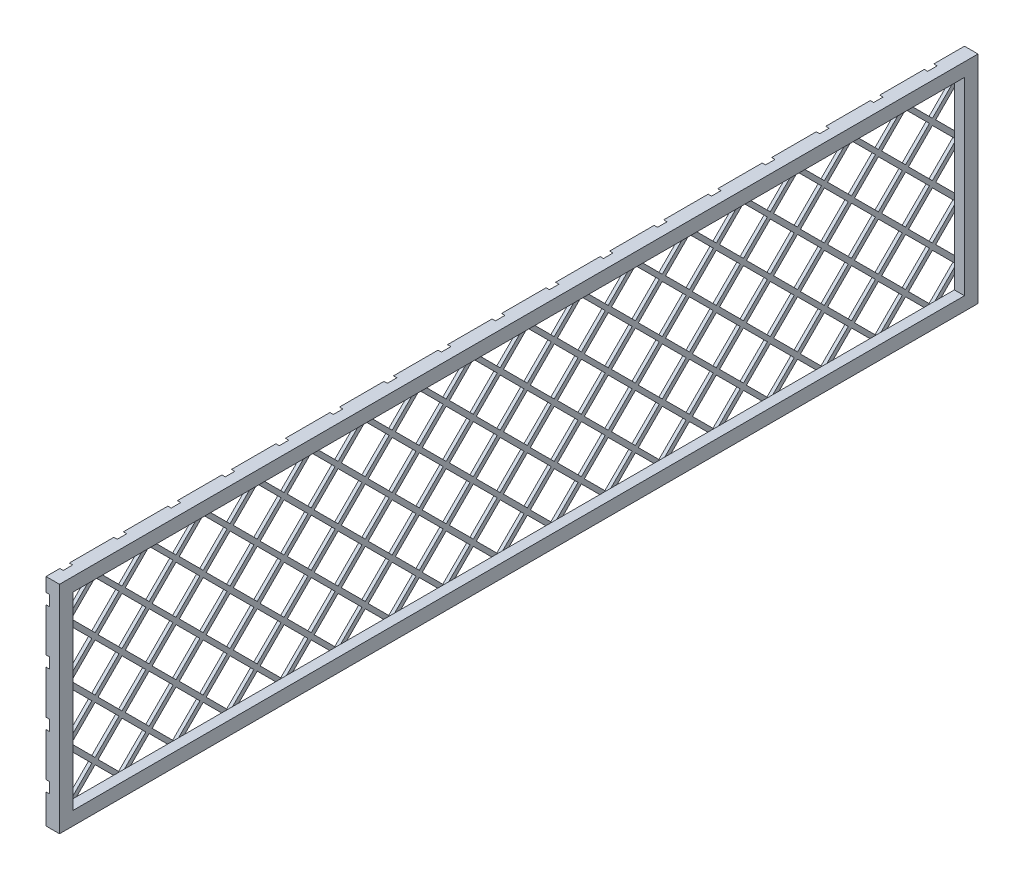
SolidWorks part; units mm, degrees
ref_plane "Front" through (0, 0, 0) normal (0, 0, 1) x (1, 0, 0)
ref_plane "Top" through (0, 0, 0) normal (0, 1, 0) x (1, 0, 0)
ref_plane "Right" through (0, 0, 0) normal (1, 0, 0) x (0, 0, -1)
sketch "Sketch1" plane through (0, 0, 0) normal (1, 0, 0) x (0, 0, -1)
  line L1 (-344.8454, 224.4468) -> (518.7546, 224.4468)
  line L2 (-344.8454, 224.4468) -> (-344.8454, 21.2468)
  line L3 (-344.8454, 21.2468) -> (518.7546, 21.2468)
  line L4 (518.7546, 224.4468) -> (518.7546, 21.2468)
  line L5 (-332.1454, 211.7468) -> (506.0546, 211.7468)
  line L6 (-332.1454, 211.7468) -> (-332.1454, 33.9468)
  line L7 (-332.1454, 33.9468) -> (506.0546, 33.9468)
  line L8 (506.0546, 211.7468) -> (506.0546, 33.9468)
  dimension "D1" = 863.6
  dimension "D2" = 203.2
  dimension "D3" = 12.7
  dimension "D4" = 12.7
  dimension "D5" = 12.7
  dimension "D6" = 12.7
extrude "Boss-Extrude1" add sketch "Sketch1" along normal blind 12.7
sketch "Sketch2" plane through (0, 0, 0) normal (-1, 0, 0) x (0, 0, 1)
  line L1 (-506.0546, 211.7468) -> (332.1454, 211.7468)
  line L2 (-506.0546, 211.7468) -> (-506.0546, 33.9468)
  line L3 (-506.0546, 33.9468) -> (332.1454, 33.9468)
  line L4 (332.1454, 211.7468) -> (332.1454, 33.9468)
extrude "Boss-Extrude2" add sketch "Sketch2" against normal blind 3.175
sketch "Sketch3" plane through (3.175, 0, 0) normal (1, 0, 0) x (0, 0, -1)
  line L0 (-324.2862, 181.2013) -> (-301.8355, 203.6519)
  line L1 (-301.8355, 203.6519) -> (-279.3849, 181.2013)
  line L2 (-324.2862, 181.2013) -> (-301.8355, 158.7506)
  line L3 (-301.8355, 158.7506) -> (-279.3849, 181.2013)
  line L4 (-276.5793, 178.1081) -> (-254.1286, 155.6575)
  line L5 (-254.1286, 155.6575) -> (-276.5793, 133.2069)
  line L6 (-276.5793, 133.2069) -> (-299.0299, 155.6575)
  line L7 (-299.0299, 155.6575) -> (-276.5793, 178.1081)
  line L8 (-327.3793, 228.9081) -> (-304.9286, 206.4575)
  line L9 (-304.9286, 206.4575) -> (-327.3793, 184.0069)
  line L10 (-327.3793, 184.0069) -> (-349.8299, 206.4575)
  line L11 (-349.8299, 206.4575) -> (-327.3793, 228.9081)
  line L12 (-276.5793, 228.9081) -> (-254.1286, 206.4575)
  line L13 (-254.1286, 206.4575) -> (-276.5793, 184.0069)
  line L14 (-276.5793, 184.0069) -> (-299.0299, 206.4575)
  line L15 (-299.0299, 206.4575) -> (-276.5793, 228.9081)
  line L16 (-254.1286, 206.4575) -> (-276.5793, 184.0069)
  line L17 (-276.5793, 184.0069) -> (-299.0299, 206.4575)
  line L18 (-299.0299, 206.4575) -> (-276.5793, 228.9081)
  line L19 (-276.5793, 228.9081) -> (-254.1286, 206.4575)
  line L20 (-251.0355, 203.6519) -> (-228.5849, 181.2013)
  line L21 (-273.4862, 181.2013) -> (-251.0355, 203.6519)
  line L22 (-273.4862, 181.2013) -> (-251.0355, 158.7506)
  line L23 (-251.0355, 158.7506) -> (-228.5849, 181.2013)
  line L24 (-203.3286, 206.4575) -> (-225.7793, 184.0069)
  line L25 (-225.7793, 184.0069) -> (-248.2299, 206.4575)
  line L26 (-248.2299, 206.4575) -> (-225.7793, 228.9081)
  line L27 (-225.7793, 228.9081) -> (-203.3286, 206.4575)
  line L28 (-200.2355, 203.6519) -> (-177.7849, 181.2013)
  line L29 (-222.6862, 181.2013) -> (-200.2355, 203.6519)
  line L30 (-222.6862, 181.2013) -> (-200.2355, 158.7506)
  line L31 (-200.2355, 158.7506) -> (-177.7849, 181.2013)
  line L32 (-152.5286, 206.4575) -> (-174.9793, 184.0069)
  line L33 (-174.9793, 184.0069) -> (-197.4299, 206.4575)
  line L34 (-197.4299, 206.4575) -> (-174.9793, 228.9081)
  line L35 (-174.9793, 228.9081) -> (-152.5286, 206.4575)
  line L36 (-149.4355, 203.6519) -> (-126.9849, 181.2013)
  line L37 (-171.8862, 181.2013) -> (-149.4355, 203.6519)
  line L38 (-171.8862, 181.2013) -> (-149.4355, 158.7506)
  line L39 (-149.4355, 158.7506) -> (-126.9849, 181.2013)
  line L40 (-101.7286, 206.4575) -> (-124.1793, 184.0069)
  line L41 (-124.1793, 184.0069) -> (-146.6299, 206.4575)
  line L42 (-146.6299, 206.4575) -> (-124.1793, 228.9081)
  line L43 (-124.1793, 228.9081) -> (-101.7286, 206.4575)
  line L44 (-98.6355, 203.6519) -> (-76.1849, 181.2013)
  line L45 (-121.0862, 181.2013) -> (-98.6355, 203.6519)
  line L46 (-121.0862, 181.2013) -> (-98.6355, 158.7506)
  line L47 (-98.6355, 158.7506) -> (-76.1849, 181.2013)
  line L48 (-50.9286, 206.4575) -> (-73.3793, 184.0069)
  line L49 (-73.3793, 184.0069) -> (-95.8299, 206.4575)
  line L50 (-95.8299, 206.4575) -> (-73.3793, 228.9081)
  line L51 (-73.3793, 228.9081) -> (-50.9286, 206.4575)
  line L52 (-47.8355, 203.6519) -> (-25.3849, 181.2013)
  line L53 (-70.2862, 181.2013) -> (-47.8355, 203.6519)
  line L54 (-70.2862, 181.2013) -> (-47.8355, 158.7506)
  line L55 (-47.8355, 158.7506) -> (-25.3849, 181.2013)
  line L56 (-0.1286, 206.4575) -> (-22.5793, 184.0069)
  line L57 (-22.5793, 184.0069) -> (-45.0299, 206.4575)
  line L58 (-45.0299, 206.4575) -> (-22.5793, 228.9081)
  line L59 (-22.5793, 228.9081) -> (-0.1286, 206.4575)
  line L60 (2.9645, 203.6519) -> (25.4151, 181.2013)
  line L61 (-19.4862, 181.2013) -> (2.9645, 203.6519)
  line L62 (-19.4862, 181.2013) -> (2.9645, 158.7506)
  line L63 (2.9645, 158.7506) -> (25.4151, 181.2013)
  line L64 (50.6714, 206.4575) -> (28.2207, 184.0069)
  line L65 (28.2207, 184.0069) -> (5.7701, 206.4575)
  line L66 (5.7701, 206.4575) -> (28.2207, 228.9081)
  line L67 (28.2207, 228.9081) -> (50.6714, 206.4575)
  line L68 (53.7645, 203.6519) -> (76.2151, 181.2013)
  line L69 (31.3138, 181.2013) -> (53.7645, 203.6519)
  line L70 (31.3138, 181.2013) -> (53.7645, 158.7506)
  line L71 (53.7645, 158.7506) -> (76.2151, 181.2013)
  line L72 (101.4714, 206.4575) -> (79.0207, 184.0069)
  line L73 (79.0207, 184.0069) -> (56.5701, 206.4575)
  line L74 (56.5701, 206.4575) -> (79.0207, 228.9081)
  line L75 (79.0207, 228.9081) -> (101.4714, 206.4575)
  line L76 (104.5645, 203.6519) -> (127.0151, 181.2013)
  line L77 (82.1138, 181.2013) -> (104.5645, 203.6519)
  line L78 (82.1138, 181.2013) -> (104.5645, 158.7506)
  line L79 (104.5645, 158.7506) -> (127.0151, 181.2013)
  line L80 (152.2714, 206.4575) -> (129.8207, 184.0069)
  line L81 (129.8207, 184.0069) -> (107.3701, 206.4575)
  line L82 (107.3701, 206.4575) -> (129.8207, 228.9081)
  line L83 (129.8207, 228.9081) -> (152.2714, 206.4575)
  line L84 (155.3645, 203.6519) -> (177.8151, 181.2013)
  line L85 (132.9138, 181.2013) -> (155.3645, 203.6519)
  line L86 (132.9138, 181.2013) -> (155.3645, 158.7506)
  line L87 (155.3645, 158.7506) -> (177.8151, 181.2013)
  line L88 (203.0714, 206.4575) -> (180.6207, 184.0069)
  line L89 (180.6207, 184.0069) -> (158.1701, 206.4575)
  line L90 (158.1701, 206.4575) -> (180.6207, 228.9081)
  line L91 (180.6207, 228.9081) -> (203.0714, 206.4575)
  line L92 (206.1645, 203.6519) -> (228.6151, 181.2013)
  line L93 (183.7138, 181.2013) -> (206.1645, 203.6519)
  line L94 (183.7138, 181.2013) -> (206.1645, 158.7506)
  line L95 (206.1645, 158.7506) -> (228.6151, 181.2013)
  line L96 (253.8714, 206.4575) -> (231.4207, 184.0069)
  line L97 (231.4207, 184.0069) -> (208.9701, 206.4575)
  line L98 (208.9701, 206.4575) -> (231.4207, 228.9081)
  line L99 (231.4207, 228.9081) -> (253.8714, 206.4575)
  line L100 (256.9645, 203.6519) -> (279.4151, 181.2013)
  line L101 (234.5138, 181.2013) -> (256.9645, 203.6519)
  line L102 (234.5138, 181.2013) -> (256.9645, 158.7506)
  line L103 (256.9645, 158.7506) -> (279.4151, 181.2013)
  line L104 (304.6714, 206.4575) -> (282.2207, 184.0069)
  line L105 (282.2207, 184.0069) -> (259.7701, 206.4575)
  line L106 (259.7701, 206.4575) -> (282.2207, 228.9081)
  line L107 (282.2207, 228.9081) -> (304.6714, 206.4575)
  line L108 (307.7645, 203.6519) -> (330.2151, 181.2013)
  line L109 (285.3138, 181.2013) -> (307.7645, 203.6519)
  line L110 (285.3138, 181.2013) -> (307.7645, 158.7506)
  line L111 (307.7645, 158.7506) -> (330.2151, 181.2013)
  line L112 (355.4714, 206.4575) -> (333.0207, 184.0069)
  line L113 (333.0207, 184.0069) -> (310.5701, 206.4575)
  line L114 (310.5701, 206.4575) -> (333.0207, 228.9081)
  line L115 (333.0207, 228.9081) -> (355.4714, 206.4575)
  line L116 (358.5645, 203.6519) -> (381.0151, 181.2013)
  line L117 (336.1138, 181.2013) -> (358.5645, 203.6519)
  line L118 (336.1138, 181.2013) -> (358.5645, 158.7506)
  line L119 (358.5645, 158.7506) -> (381.0151, 181.2013)
  line L120 (406.2714, 206.4575) -> (383.8207, 184.0069)
  line L121 (383.8207, 184.0069) -> (361.3701, 206.4575)
  line L122 (361.3701, 206.4575) -> (383.8207, 228.9081)
  line L123 (383.8207, 228.9081) -> (406.2714, 206.4575)
  line L124 (409.3645, 203.6519) -> (431.8151, 181.2013)
  line L125 (386.9138, 181.2013) -> (409.3645, 203.6519)
  line L126 (386.9138, 181.2013) -> (409.3645, 158.7506)
  line L127 (409.3645, 158.7506) -> (431.8151, 181.2013)
  line L128 (457.0714, 206.4575) -> (434.6207, 184.0069)
  line L129 (434.6207, 184.0069) -> (412.1701, 206.4575)
  line L130 (412.1701, 206.4575) -> (434.6207, 228.9081)
  line L131 (434.6207, 228.9081) -> (457.0714, 206.4575)
  line L132 (460.1645, 203.6519) -> (482.6151, 181.2013)
  line L133 (437.7138, 181.2013) -> (460.1645, 203.6519)
  line L134 (437.7138, 181.2013) -> (460.1645, 158.7506)
  line L135 (460.1645, 158.7506) -> (482.6151, 181.2013)
  line L136 (507.8714, 206.4575) -> (485.4207, 184.0069)
  line L137 (485.4207, 184.0069) -> (462.9701, 206.4575)
  line L138 (462.9701, 206.4575) -> (485.4207, 228.9081)
  line L139 (485.4207, 228.9081) -> (507.8714, 206.4575)
  line L140 (510.9645, 203.6519) -> (533.4151, 181.2013)
  line L141 (488.5138, 181.2013) -> (510.9645, 203.6519)
  line L142 (488.5138, 181.2013) -> (510.9645, 158.7506)
  line L143 (510.9645, 158.7506) -> (533.4151, 181.2013)
  line L144 (-254.1286, 155.6575) -> (-276.5793, 133.2069)
  line L145 (-276.5793, 133.2069) -> (-299.0299, 155.6575)
  line L146 (-299.0299, 155.6575) -> (-276.5793, 178.1081)
  line L147 (-276.5793, 178.1081) -> (-254.1286, 155.6575)
  line L148 (-251.0355, 152.8519) -> (-228.5849, 130.4013)
  line L149 (-273.4862, 130.4013) -> (-251.0355, 152.8519)
  line L150 (-273.4862, 130.4013) -> (-251.0355, 107.9506)
  line L151 (-251.0355, 107.9506) -> (-228.5849, 130.4013)
  line L152 (-203.3286, 155.6575) -> (-225.7793, 133.2069)
  line L153 (-225.7793, 133.2069) -> (-248.2299, 155.6575)
  line L154 (-248.2299, 155.6575) -> (-225.7793, 178.1081)
  line L155 (-225.7793, 178.1081) -> (-203.3286, 155.6575)
  line L156 (-200.2355, 152.8519) -> (-177.7849, 130.4013)
  line L157 (-222.6862, 130.4013) -> (-200.2355, 152.8519)
  line L158 (-222.6862, 130.4013) -> (-200.2355, 107.9506)
  line L159 (-200.2355, 107.9506) -> (-177.7849, 130.4013)
  line L160 (-152.5286, 155.6575) -> (-174.9793, 133.2069)
  line L161 (-174.9793, 133.2069) -> (-197.4299, 155.6575)
  line L162 (-197.4299, 155.6575) -> (-174.9793, 178.1081)
  line L163 (-174.9793, 178.1081) -> (-152.5286, 155.6575)
  line L164 (-149.4355, 152.8519) -> (-126.9849, 130.4013)
  line L165 (-171.8862, 130.4013) -> (-149.4355, 152.8519)
  line L166 (-171.8862, 130.4013) -> (-149.4355, 107.9506)
  line L167 (-149.4355, 107.9506) -> (-126.9849, 130.4013)
  line L168 (-101.7286, 155.6575) -> (-124.1793, 133.2069)
  line L169 (-124.1793, 133.2069) -> (-146.6299, 155.6575)
  line L170 (-146.6299, 155.6575) -> (-124.1793, 178.1081)
  line L171 (-124.1793, 178.1081) -> (-101.7286, 155.6575)
  line L172 (-98.6355, 152.8519) -> (-76.1849, 130.4013)
  line L173 (-121.0862, 130.4013) -> (-98.6355, 152.8519)
  line L174 (-121.0862, 130.4013) -> (-98.6355, 107.9506)
  line L175 (-98.6355, 107.9506) -> (-76.1849, 130.4013)
  line L176 (-50.9286, 155.6575) -> (-73.3793, 133.2069)
  line L177 (-73.3793, 133.2069) -> (-95.8299, 155.6575)
  line L178 (-95.8299, 155.6575) -> (-73.3793, 178.1081)
  line L179 (-73.3793, 178.1081) -> (-50.9286, 155.6575)
  line L180 (-47.8355, 152.8519) -> (-25.3849, 130.4013)
  line L181 (-70.2862, 130.4013) -> (-47.8355, 152.8519)
  line L182 (-70.2862, 130.4013) -> (-47.8355, 107.9506)
  line L183 (-47.8355, 107.9506) -> (-25.3849, 130.4013)
  line L184 (-0.1286, 155.6575) -> (-22.5793, 133.2069)
  line L185 (-22.5793, 133.2069) -> (-45.0299, 155.6575)
  line L186 (-45.0299, 155.6575) -> (-22.5793, 178.1081)
  line L187 (-22.5793, 178.1081) -> (-0.1286, 155.6575)
  line L188 (2.9645, 152.8519) -> (25.4151, 130.4013)
  line L189 (-19.4862, 130.4013) -> (2.9645, 152.8519)
  line L190 (-19.4862, 130.4013) -> (2.9645, 107.9506)
  line L191 (2.9645, 107.9506) -> (25.4151, 130.4013)
  line L192 (50.6714, 155.6575) -> (28.2207, 133.2069)
  line L193 (28.2207, 133.2069) -> (5.7701, 155.6575)
  line L194 (5.7701, 155.6575) -> (28.2207, 178.1081)
  line L195 (28.2207, 178.1081) -> (50.6714, 155.6575)
  line L196 (53.7645, 152.8519) -> (76.2151, 130.4013)
  line L197 (31.3138, 130.4013) -> (53.7645, 152.8519)
  line L198 (31.3138, 130.4013) -> (53.7645, 107.9506)
  line L199 (53.7645, 107.9506) -> (76.2151, 130.4013)
  line L200 (101.4714, 155.6575) -> (79.0207, 133.2069)
  line L201 (79.0207, 133.2069) -> (56.5701, 155.6575)
  line L202 (56.5701, 155.6575) -> (79.0207, 178.1081)
  line L203 (79.0207, 178.1081) -> (101.4714, 155.6575)
  line L204 (104.5645, 152.8519) -> (127.0151, 130.4013)
  line L205 (82.1138, 130.4013) -> (104.5645, 152.8519)
  line L206 (82.1138, 130.4013) -> (104.5645, 107.9506)
  line L207 (104.5645, 107.9506) -> (127.0151, 130.4013)
  line L208 (152.2714, 155.6575) -> (129.8207, 133.2069)
  line L209 (129.8207, 133.2069) -> (107.3701, 155.6575)
  line L210 (107.3701, 155.6575) -> (129.8207, 178.1081)
  line L211 (129.8207, 178.1081) -> (152.2714, 155.6575)
  line L212 (155.3645, 152.8519) -> (177.8151, 130.4013)
  line L213 (132.9138, 130.4013) -> (155.3645, 152.8519)
  line L214 (132.9138, 130.4013) -> (155.3645, 107.9506)
  line L215 (155.3645, 107.9506) -> (177.8151, 130.4013)
  line L216 (203.0714, 155.6575) -> (180.6207, 133.2069)
  line L217 (180.6207, 133.2069) -> (158.1701, 155.6575)
  line L218 (158.1701, 155.6575) -> (180.6207, 178.1081)
  line L219 (180.6207, 178.1081) -> (203.0714, 155.6575)
  line L220 (206.1645, 152.8519) -> (228.6151, 130.4013)
  line L221 (183.7138, 130.4013) -> (206.1645, 152.8519)
  line L222 (183.7138, 130.4013) -> (206.1645, 107.9506)
  line L223 (206.1645, 107.9506) -> (228.6151, 130.4013)
  line L224 (253.8714, 155.6575) -> (231.4207, 133.2069)
  line L225 (231.4207, 133.2069) -> (208.9701, 155.6575)
  line L226 (208.9701, 155.6575) -> (231.4207, 178.1081)
  line L227 (231.4207, 178.1081) -> (253.8714, 155.6575)
  line L228 (256.9645, 152.8519) -> (279.4151, 130.4013)
  line L229 (234.5138, 130.4013) -> (256.9645, 152.8519)
  line L230 (234.5138, 130.4013) -> (256.9645, 107.9506)
  line L231 (256.9645, 107.9506) -> (279.4151, 130.4013)
  line L232 (304.6714, 155.6575) -> (282.2207, 133.2069)
  line L233 (282.2207, 133.2069) -> (259.7701, 155.6575)
  line L234 (259.7701, 155.6575) -> (282.2207, 178.1081)
  line L235 (282.2207, 178.1081) -> (304.6714, 155.6575)
  line L236 (307.7645, 152.8519) -> (330.2151, 130.4013)
  line L237 (285.3138, 130.4013) -> (307.7645, 152.8519)
  line L238 (285.3138, 130.4013) -> (307.7645, 107.9506)
  line L239 (307.7645, 107.9506) -> (330.2151, 130.4013)
  line L240 (355.4714, 155.6575) -> (333.0207, 133.2069)
  line L241 (333.0207, 133.2069) -> (310.5701, 155.6575)
  line L242 (310.5701, 155.6575) -> (333.0207, 178.1081)
  line L243 (333.0207, 178.1081) -> (355.4714, 155.6575)
  line L244 (358.5645, 152.8519) -> (381.0151, 130.4013)
  line L245 (336.1138, 130.4013) -> (358.5645, 152.8519)
  line L246 (336.1138, 130.4013) -> (358.5645, 107.9506)
  line L247 (358.5645, 107.9506) -> (381.0151, 130.4013)
  line L248 (406.2714, 155.6575) -> (383.8207, 133.2069)
  line L249 (383.8207, 133.2069) -> (361.3701, 155.6575)
  line L250 (361.3701, 155.6575) -> (383.8207, 178.1081)
  line L251 (383.8207, 178.1081) -> (406.2714, 155.6575)
  line L252 (409.3645, 152.8519) -> (431.8151, 130.4013)
  line L253 (386.9138, 130.4013) -> (409.3645, 152.8519)
  line L254 (386.9138, 130.4013) -> (409.3645, 107.9506)
  line L255 (409.3645, 107.9506) -> (431.8151, 130.4013)
  line L256 (457.0714, 155.6575) -> (434.6207, 133.2069)
  line L257 (434.6207, 133.2069) -> (412.1701, 155.6575)
  line L258 (412.1701, 155.6575) -> (434.6207, 178.1081)
  line L259 (434.6207, 178.1081) -> (457.0714, 155.6575)
  line L260 (460.1645, 152.8519) -> (482.6151, 130.4013)
  line L261 (437.7138, 130.4013) -> (460.1645, 152.8519)
  line L262 (437.7138, 130.4013) -> (460.1645, 107.9506)
  line L263 (460.1645, 107.9506) -> (482.6151, 130.4013)
  line L264 (507.8714, 155.6575) -> (485.4207, 133.2069)
  line L265 (485.4207, 133.2069) -> (462.9701, 155.6575)
  line L266 (462.9701, 155.6575) -> (485.4207, 178.1081)
  line L267 (485.4207, 178.1081) -> (507.8714, 155.6575)
  line L268 (510.9645, 152.8519) -> (533.4151, 130.4013)
  line L269 (488.5138, 130.4013) -> (510.9645, 152.8519)
  line L270 (488.5138, 130.4013) -> (510.9645, 107.9506)
  line L271 (510.9645, 107.9506) -> (533.4151, 130.4013)
  line L272 (-254.1286, 104.8575) -> (-276.5793, 82.4069)
  line L273 (-276.5793, 82.4069) -> (-299.0299, 104.8575)
  line L274 (-299.0299, 104.8575) -> (-276.5793, 127.3081)
  line L275 (-276.5793, 127.3081) -> (-254.1286, 104.8575)
  line L276 (-251.0355, 102.0519) -> (-228.5849, 79.6013)
  line L277 (-273.4862, 79.6013) -> (-251.0355, 102.0519)
  line L278 (-273.4862, 79.6013) -> (-251.0355, 57.1506)
  line L279 (-251.0355, 57.1506) -> (-228.5849, 79.6013)
  line L280 (-203.3286, 104.8575) -> (-225.7793, 82.4069)
  line L281 (-225.7793, 82.4069) -> (-248.2299, 104.8575)
  line L282 (-248.2299, 104.8575) -> (-225.7793, 127.3081)
  line L283 (-225.7793, 127.3081) -> (-203.3286, 104.8575)
  line L284 (-200.2355, 102.0519) -> (-177.7849, 79.6013)
  line L285 (-222.6862, 79.6013) -> (-200.2355, 102.0519)
  line L286 (-222.6862, 79.6013) -> (-200.2355, 57.1506)
  line L287 (-200.2355, 57.1506) -> (-177.7849, 79.6013)
  line L288 (-152.5286, 104.8575) -> (-174.9793, 82.4069)
  line L289 (-174.9793, 82.4069) -> (-197.4299, 104.8575)
  line L290 (-197.4299, 104.8575) -> (-174.9793, 127.3081)
  line L291 (-174.9793, 127.3081) -> (-152.5286, 104.8575)
  line L292 (-149.4355, 102.0519) -> (-126.9849, 79.6013)
  line L293 (-171.8862, 79.6013) -> (-149.4355, 102.0519)
  line L294 (-171.8862, 79.6013) -> (-149.4355, 57.1506)
  line L295 (-149.4355, 57.1506) -> (-126.9849, 79.6013)
  line L296 (-101.7286, 104.8575) -> (-124.1793, 82.4069)
  line L297 (-124.1793, 82.4069) -> (-146.6299, 104.8575)
  line L298 (-146.6299, 104.8575) -> (-124.1793, 127.3081)
  line L299 (-124.1793, 127.3081) -> (-101.7286, 104.8575)
  line L300 (-98.6355, 102.0519) -> (-76.1849, 79.6013)
  line L301 (-121.0862, 79.6013) -> (-98.6355, 102.0519)
  line L302 (-121.0862, 79.6013) -> (-98.6355, 57.1506)
  line L303 (-98.6355, 57.1506) -> (-76.1849, 79.6013)
  line L304 (-50.9286, 104.8575) -> (-73.3793, 82.4069)
  line L305 (-73.3793, 82.4069) -> (-95.8299, 104.8575)
  line L306 (-95.8299, 104.8575) -> (-73.3793, 127.3081)
  line L307 (-73.3793, 127.3081) -> (-50.9286, 104.8575)
  line L308 (-47.8355, 102.0519) -> (-25.3849, 79.6013)
  line L309 (-70.2862, 79.6013) -> (-47.8355, 102.0519)
  line L310 (-70.2862, 79.6013) -> (-47.8355, 57.1506)
  line L311 (-47.8355, 57.1506) -> (-25.3849, 79.6013)
  line L312 (-0.1286, 104.8575) -> (-22.5793, 82.4069)
  line L313 (-22.5793, 82.4069) -> (-45.0299, 104.8575)
  line L314 (-45.0299, 104.8575) -> (-22.5793, 127.3081)
  line L315 (-22.5793, 127.3081) -> (-0.1286, 104.8575)
  line L316 (2.9645, 102.0519) -> (25.4151, 79.6013)
  line L317 (-19.4862, 79.6013) -> (2.9645, 102.0519)
  line L318 (-19.4862, 79.6013) -> (2.9645, 57.1506)
  line L319 (2.9645, 57.1506) -> (25.4151, 79.6013)
  line L320 (50.6714, 104.8575) -> (28.2207, 82.4069)
  line L321 (28.2207, 82.4069) -> (5.7701, 104.8575)
  line L322 (5.7701, 104.8575) -> (28.2207, 127.3081)
  line L323 (28.2207, 127.3081) -> (50.6714, 104.8575)
  line L324 (53.7645, 102.0519) -> (76.2151, 79.6013)
  line L325 (31.3138, 79.6013) -> (53.7645, 102.0519)
  line L326 (31.3138, 79.6013) -> (53.7645, 57.1506)
  line L327 (53.7645, 57.1506) -> (76.2151, 79.6013)
  line L328 (101.4714, 104.8575) -> (79.0207, 82.4069)
  line L329 (79.0207, 82.4069) -> (56.5701, 104.8575)
  line L330 (56.5701, 104.8575) -> (79.0207, 127.3081)
  line L331 (79.0207, 127.3081) -> (101.4714, 104.8575)
  line L332 (104.5645, 102.0519) -> (127.0151, 79.6013)
  line L333 (82.1138, 79.6013) -> (104.5645, 102.0519)
  line L334 (82.1138, 79.6013) -> (104.5645, 57.1506)
  line L335 (104.5645, 57.1506) -> (127.0151, 79.6013)
  line L336 (152.2714, 104.8575) -> (129.8207, 82.4069)
  line L337 (129.8207, 82.4069) -> (107.3701, 104.8575)
  line L338 (107.3701, 104.8575) -> (129.8207, 127.3081)
  line L339 (129.8207, 127.3081) -> (152.2714, 104.8575)
  line L340 (155.3645, 102.0519) -> (177.8151, 79.6013)
  line L341 (132.9138, 79.6013) -> (155.3645, 102.0519)
  line L342 (132.9138, 79.6013) -> (155.3645, 57.1506)
  line L343 (155.3645, 57.1506) -> (177.8151, 79.6013)
  line L344 (203.0714, 104.8575) -> (180.6207, 82.4069)
  line L345 (180.6207, 82.4069) -> (158.1701, 104.8575)
  line L346 (158.1701, 104.8575) -> (180.6207, 127.3081)
  line L347 (180.6207, 127.3081) -> (203.0714, 104.8575)
  line L348 (206.1645, 102.0519) -> (228.6151, 79.6013)
  line L349 (183.7138, 79.6013) -> (206.1645, 102.0519)
  line L350 (183.7138, 79.6013) -> (206.1645, 57.1506)
  line L351 (206.1645, 57.1506) -> (228.6151, 79.6013)
  line L352 (253.8714, 104.8575) -> (231.4207, 82.4069)
  line L353 (231.4207, 82.4069) -> (208.9701, 104.8575)
  line L354 (208.9701, 104.8575) -> (231.4207, 127.3081)
  line L355 (231.4207, 127.3081) -> (253.8714, 104.8575)
  line L356 (256.9645, 102.0519) -> (279.4151, 79.6013)
  line L357 (234.5138, 79.6013) -> (256.9645, 102.0519)
  line L358 (234.5138, 79.6013) -> (256.9645, 57.1506)
  line L359 (256.9645, 57.1506) -> (279.4151, 79.6013)
  line L360 (304.6714, 104.8575) -> (282.2207, 82.4069)
  line L361 (282.2207, 82.4069) -> (259.7701, 104.8575)
  line L362 (259.7701, 104.8575) -> (282.2207, 127.3081)
  line L363 (282.2207, 127.3081) -> (304.6714, 104.8575)
  line L364 (307.7645, 102.0519) -> (330.2151, 79.6013)
  line L365 (285.3138, 79.6013) -> (307.7645, 102.0519)
  line L366 (285.3138, 79.6013) -> (307.7645, 57.1506)
  line L367 (307.7645, 57.1506) -> (330.2151, 79.6013)
  line L368 (355.4714, 104.8575) -> (333.0207, 82.4069)
  line L369 (333.0207, 82.4069) -> (310.5701, 104.8575)
  line L370 (310.5701, 104.8575) -> (333.0207, 127.3081)
  line L371 (333.0207, 127.3081) -> (355.4714, 104.8575)
  line L372 (358.5645, 102.0519) -> (381.0151, 79.6013)
  line L373 (336.1138, 79.6013) -> (358.5645, 102.0519)
  line L374 (336.1138, 79.6013) -> (358.5645, 57.1506)
  line L375 (358.5645, 57.1506) -> (381.0151, 79.6013)
  line L376 (406.2714, 104.8575) -> (383.8207, 82.4069)
  line L377 (383.8207, 82.4069) -> (361.3701, 104.8575)
  line L378 (361.3701, 104.8575) -> (383.8207, 127.3081)
  line L379 (383.8207, 127.3081) -> (406.2714, 104.8575)
  line L380 (409.3645, 102.0519) -> (431.8151, 79.6013)
  line L381 (386.9138, 79.6013) -> (409.3645, 102.0519)
  line L382 (386.9138, 79.6013) -> (409.3645, 57.1506)
  line L383 (409.3645, 57.1506) -> (431.8151, 79.6013)
  line L384 (457.0714, 104.8575) -> (434.6207, 82.4069)
  line L385 (434.6207, 82.4069) -> (412.1701, 104.8575)
  line L386 (412.1701, 104.8575) -> (434.6207, 127.3081)
  line L387 (434.6207, 127.3081) -> (457.0714, 104.8575)
  line L388 (460.1645, 102.0519) -> (482.6151, 79.6013)
  line L389 (437.7138, 79.6013) -> (460.1645, 102.0519)
  line L390 (437.7138, 79.6013) -> (460.1645, 57.1506)
  line L391 (460.1645, 57.1506) -> (482.6151, 79.6013)
  line L392 (507.8714, 104.8575) -> (485.4207, 82.4069)
  line L393 (485.4207, 82.4069) -> (462.9701, 104.8575)
  line L394 (462.9701, 104.8575) -> (485.4207, 127.3081)
  line L395 (485.4207, 127.3081) -> (507.8714, 104.8575)
  line L396 (510.9645, 102.0519) -> (533.4151, 79.6013)
  line L397 (488.5138, 79.6013) -> (510.9645, 102.0519)
  line L398 (488.5138, 79.6013) -> (510.9645, 57.1506)
  line L399 (510.9645, 57.1506) -> (533.4151, 79.6013)
  line L400 (-254.1286, 54.0575) -> (-276.5793, 31.6069)
  line L401 (-276.5793, 31.6069) -> (-299.0299, 54.0575)
  line L402 (-299.0299, 54.0575) -> (-276.5793, 76.5081)
  line L403 (-276.5793, 76.5081) -> (-254.1286, 54.0575)
  line L404 (-251.0355, 51.2519) -> (-228.5849, 28.8013)
  line L405 (-273.4862, 28.8013) -> (-251.0355, 51.2519)
  line L406 (-273.4862, 28.8013) -> (-251.0355, 6.3506)
  line L407 (-251.0355, 6.3506) -> (-228.5849, 28.8013)
  line L408 (-203.3286, 54.0575) -> (-225.7793, 31.6069)
  line L409 (-225.7793, 31.6069) -> (-248.2299, 54.0575)
  line L410 (-248.2299, 54.0575) -> (-225.7793, 76.5081)
  line L411 (-225.7793, 76.5081) -> (-203.3286, 54.0575)
  line L412 (-200.2355, 51.2519) -> (-177.7849, 28.8013)
  line L413 (-222.6862, 28.8013) -> (-200.2355, 51.2519)
  line L414 (-222.6862, 28.8013) -> (-200.2355, 6.3506)
  line L415 (-200.2355, 6.3506) -> (-177.7849, 28.8013)
  line L416 (-152.5286, 54.0575) -> (-174.9793, 31.6069)
  line L417 (-174.9793, 31.6069) -> (-197.4299, 54.0575)
  line L418 (-197.4299, 54.0575) -> (-174.9793, 76.5081)
  line L419 (-174.9793, 76.5081) -> (-152.5286, 54.0575)
  line L420 (-149.4355, 51.2519) -> (-126.9849, 28.8013)
  line L421 (-171.8862, 28.8013) -> (-149.4355, 51.2519)
  line L422 (-171.8862, 28.8013) -> (-149.4355, 6.3506)
  line L423 (-149.4355, 6.3506) -> (-126.9849, 28.8013)
  line L424 (-101.7286, 54.0575) -> (-124.1793, 31.6069)
  line L425 (-124.1793, 31.6069) -> (-146.6299, 54.0575)
  line L426 (-146.6299, 54.0575) -> (-124.1793, 76.5081)
  line L427 (-124.1793, 76.5081) -> (-101.7286, 54.0575)
  line L428 (-98.6355, 51.2519) -> (-76.1849, 28.8013)
  line L429 (-121.0862, 28.8013) -> (-98.6355, 51.2519)
  line L430 (-121.0862, 28.8013) -> (-98.6355, 6.3506)
  line L431 (-98.6355, 6.3506) -> (-76.1849, 28.8013)
  line L432 (-50.9286, 54.0575) -> (-73.3793, 31.6069)
  line L433 (-73.3793, 31.6069) -> (-95.8299, 54.0575)
  line L434 (-95.8299, 54.0575) -> (-73.3793, 76.5081)
  line L435 (-73.3793, 76.5081) -> (-50.9286, 54.0575)
  line L436 (-47.8355, 51.2519) -> (-25.3849, 28.8013)
  line L437 (-70.2862, 28.8013) -> (-47.8355, 51.2519)
  line L438 (-70.2862, 28.8013) -> (-47.8355, 6.3506)
  line L439 (-47.8355, 6.3506) -> (-25.3849, 28.8013)
  line L440 (-0.1286, 54.0575) -> (-22.5793, 31.6069)
  line L441 (-22.5793, 31.6069) -> (-45.0299, 54.0575)
  line L442 (-45.0299, 54.0575) -> (-22.5793, 76.5081)
  line L443 (-22.5793, 76.5081) -> (-0.1286, 54.0575)
  line L444 (2.9645, 51.2519) -> (25.4151, 28.8013)
  line L445 (-19.4862, 28.8013) -> (2.9645, 51.2519)
  line L446 (-19.4862, 28.8013) -> (2.9645, 6.3506)
  line L447 (2.9645, 6.3506) -> (25.4151, 28.8013)
  line L448 (50.6714, 54.0575) -> (28.2207, 31.6069)
  line L449 (28.2207, 31.6069) -> (5.7701, 54.0575)
  line L450 (5.7701, 54.0575) -> (28.2207, 76.5081)
  line L451 (28.2207, 76.5081) -> (50.6714, 54.0575)
  line L452 (53.7645, 51.2519) -> (76.2151, 28.8013)
  line L453 (31.3138, 28.8013) -> (53.7645, 51.2519)
  line L454 (31.3138, 28.8013) -> (53.7645, 6.3506)
  line L455 (53.7645, 6.3506) -> (76.2151, 28.8013)
  line L456 (101.4714, 54.0575) -> (79.0207, 31.6069)
  line L457 (79.0207, 31.6069) -> (56.5701, 54.0575)
  line L458 (56.5701, 54.0575) -> (79.0207, 76.5081)
  line L459 (79.0207, 76.5081) -> (101.4714, 54.0575)
  line L460 (104.5645, 51.2519) -> (127.0151, 28.8013)
  line L461 (82.1138, 28.8013) -> (104.5645, 51.2519)
  line L462 (82.1138, 28.8013) -> (104.5645, 6.3506)
  line L463 (104.5645, 6.3506) -> (127.0151, 28.8013)
  line L464 (152.2714, 54.0575) -> (129.8207, 31.6069)
  line L465 (129.8207, 31.6069) -> (107.3701, 54.0575)
  line L466 (107.3701, 54.0575) -> (129.8207, 76.5081)
  line L467 (129.8207, 76.5081) -> (152.2714, 54.0575)
  line L468 (155.3645, 51.2519) -> (177.8151, 28.8013)
  line L469 (132.9138, 28.8013) -> (155.3645, 51.2519)
  line L470 (132.9138, 28.8013) -> (155.3645, 6.3506)
  line L471 (155.3645, 6.3506) -> (177.8151, 28.8013)
  line L472 (203.0714, 54.0575) -> (180.6207, 31.6069)
  line L473 (180.6207, 31.6069) -> (158.1701, 54.0575)
  line L474 (158.1701, 54.0575) -> (180.6207, 76.5081)
  line L475 (180.6207, 76.5081) -> (203.0714, 54.0575)
  line L476 (206.1645, 51.2519) -> (228.6151, 28.8013)
  line L477 (183.7138, 28.8013) -> (206.1645, 51.2519)
  line L478 (183.7138, 28.8013) -> (206.1645, 6.3506)
  line L479 (206.1645, 6.3506) -> (228.6151, 28.8013)
  line L480 (253.8714, 54.0575) -> (231.4207, 31.6069)
  line L481 (231.4207, 31.6069) -> (208.9701, 54.0575)
  line L482 (208.9701, 54.0575) -> (231.4207, 76.5081)
  line L483 (231.4207, 76.5081) -> (253.8714, 54.0575)
  line L484 (256.9645, 51.2519) -> (279.4151, 28.8013)
  line L485 (234.5138, 28.8013) -> (256.9645, 51.2519)
  line L486 (234.5138, 28.8013) -> (256.9645, 6.3506)
  line L487 (256.9645, 6.3506) -> (279.4151, 28.8013)
  line L488 (304.6714, 54.0575) -> (282.2207, 31.6069)
  line L489 (282.2207, 31.6069) -> (259.7701, 54.0575)
  line L490 (259.7701, 54.0575) -> (282.2207, 76.5081)
  line L491 (282.2207, 76.5081) -> (304.6714, 54.0575)
  line L492 (307.7645, 51.2519) -> (330.2151, 28.8013)
  line L493 (285.3138, 28.8013) -> (307.7645, 51.2519)
  line L494 (285.3138, 28.8013) -> (307.7645, 6.3506)
  line L495 (307.7645, 6.3506) -> (330.2151, 28.8013)
  line L496 (355.4714, 54.0575) -> (333.0207, 31.6069)
  line L497 (333.0207, 31.6069) -> (310.5701, 54.0575)
  line L498 (310.5701, 54.0575) -> (333.0207, 76.5081)
  line L499 (333.0207, 76.5081) -> (355.4714, 54.0575)
  line L500 (358.5645, 51.2519) -> (381.0151, 28.8013)
  line L501 (336.1138, 28.8013) -> (358.5645, 51.2519)
  line L502 (336.1138, 28.8013) -> (358.5645, 6.3506)
  line L503 (358.5645, 6.3506) -> (381.0151, 28.8013)
  line L504 (406.2714, 54.0575) -> (383.8207, 31.6069)
  line L505 (383.8207, 31.6069) -> (361.3701, 54.0575)
  line L506 (361.3701, 54.0575) -> (383.8207, 76.5081)
  line L507 (383.8207, 76.5081) -> (406.2714, 54.0575)
  line L508 (409.3645, 51.2519) -> (431.8151, 28.8013)
  line L509 (386.9138, 28.8013) -> (409.3645, 51.2519)
  line L510 (386.9138, 28.8013) -> (409.3645, 6.3506)
  line L511 (409.3645, 6.3506) -> (431.8151, 28.8013)
  line L512 (457.0714, 54.0575) -> (434.6207, 31.6069)
  line L513 (434.6207, 31.6069) -> (412.1701, 54.0575)
  line L514 (412.1701, 54.0575) -> (434.6207, 76.5081)
  line L515 (434.6207, 76.5081) -> (457.0714, 54.0575)
  line L516 (460.1645, 51.2519) -> (482.6151, 28.8013)
  line L517 (437.7138, 28.8013) -> (460.1645, 51.2519)
  line L518 (437.7138, 28.8013) -> (460.1645, 6.3506)
  line L519 (460.1645, 6.3506) -> (482.6151, 28.8013)
  line L520 (507.8714, 54.0575) -> (485.4207, 31.6069)
  line L521 (485.4207, 31.6069) -> (462.9701, 54.0575)
  line L522 (462.9701, 54.0575) -> (485.4207, 76.5081)
  line L523 (485.4207, 76.5081) -> (507.8714, 54.0575)
  line L524 (510.9645, 51.2519) -> (533.4151, 28.8013)
  line L525 (488.5138, 28.8013) -> (510.9645, 51.2519)
  line L526 (488.5138, 28.8013) -> (510.9645, 6.3506)
  line L527 (510.9645, 6.3506) -> (533.4151, 28.8013)
  line L528 (-304.9286, 155.6575) -> (-327.3793, 133.2069)
  line L529 (-327.3793, 133.2069) -> (-349.8299, 155.6575)
  line L530 (-349.8299, 155.6575) -> (-327.3793, 178.1081)
  line L531 (-327.3793, 178.1081) -> (-304.9286, 155.6575)
  line L532 (-301.8355, 152.8519) -> (-279.3849, 130.4013)
  line L533 (-324.2862, 130.4013) -> (-301.8355, 152.8519)
  line L534 (-324.2862, 130.4013) -> (-301.8355, 107.9506)
  line L535 (-301.8355, 107.9506) -> (-279.3849, 130.4013)
  line L536 (-304.9286, 104.8575) -> (-327.3793, 82.4069)
  line L537 (-327.3793, 82.4069) -> (-349.8299, 104.8575)
  line L538 (-349.8299, 104.8575) -> (-327.3793, 127.3081)
  line L539 (-327.3793, 127.3081) -> (-304.9286, 104.8575)
  line L540 (-301.8355, 102.0519) -> (-279.3849, 79.6013)
  line L541 (-324.2862, 79.6013) -> (-301.8355, 102.0519)
  line L542 (-324.2862, 79.6013) -> (-301.8355, 57.1506)
  line L543 (-301.8355, 57.1506) -> (-279.3849, 79.6013)
  line L544 (-304.9286, 54.0575) -> (-327.3793, 31.6069)
  line L545 (-327.3793, 31.6069) -> (-349.8299, 54.0575)
  line L546 (-349.8299, 54.0575) -> (-327.3793, 76.5081)
  line L547 (-327.3793, 76.5081) -> (-304.9286, 54.0575)
  line L548 (-301.8355, 51.2519) -> (-279.3849, 28.8013)
  line L549 (-324.2862, 28.8013) -> (-301.8355, 51.2519)
  line L550 (-324.2862, 28.8013) -> (-301.8355, 6.3506)
  line L551 (-301.8355, 6.3506) -> (-279.3849, 28.8013)
  dimension "D1" = 17
  dimension "D2" = 4
extrude "Cut-Extrude1" cut sketch "Sketch3" against normal blind 3.175
